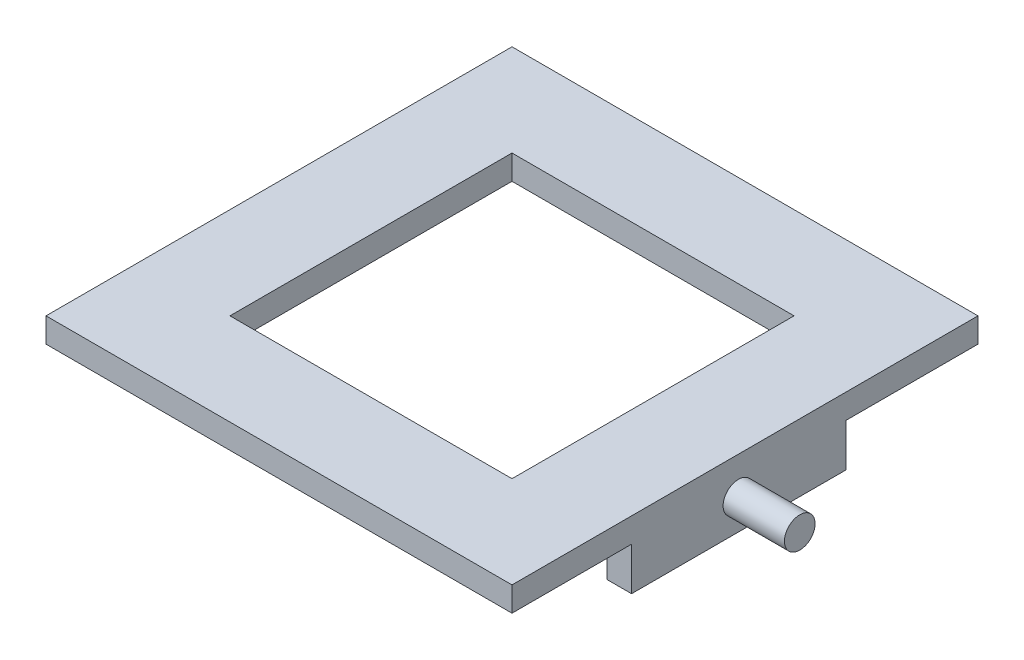
SolidWorks part; units mm, degrees
ref_plane "Front Plane" through (0, 0, 0) normal (0, 0, 1) x (1, 0, 0)
ref_plane "Top Plane" through (0, 0, 0) normal (0, 1, 0) x (1, 0, 0)
ref_plane "Right Plane" through (0, 0, 0) normal (1, 0, 0) x (0, 0, -1)
sketch "Sketch1" plane through (0, 0, 0) normal (0, 1, 0) x (1, 0, 0)
  line L0 (15, 15) -> (15, 61)
  line L1 (0, 0) -> (76, 0)
  line L2 (0, 0) -> (0, 76)
  line L3 (0, 76) -> (76, 76)
  line L4 (76, 0) -> (76, 76)
  line L5 (15, 61) -> (61, 61)
  line L6 (61, 15) -> (61, 61)
  line L7 (15, 15) -> (61, 15)
  dimension "D1" = 76
  dimension "D2" = 76
  dimension "D3" = 15
extrude "Boss-Extrude2" add sketch "Sketch1" along normal blind 4
sketch "Sketch3" plane through (0, 0, 0) normal (-1, 0, 0) x (0, 0, 1)
sketch "Sketch7" plane through (0, 0, 0) normal (-1, 0, 0) x (0, 0, 1)
  line L0 (-76, 4) -> (0, 4) construction
  line L1 (-54.5, 4) -> (-19.5, 4)
  line L2 (-54.5, 4) -> (-54.5, -7)
  line L3 (-54.5, -7) -> (-19.5, -7)
  line L4 (-19.5, 4) -> (-19.5, -7)
  line L9 (-51.45, -2.06) -> (-22.55, -2.06)
  circle A4 centre (-51.45, -2.06) radius 0.6
  circle A5 centre (-22.55, -2.06) radius 0.6
  point P6 (-37, -2.06)
  point P7 (-37, 4)
  point P13 (-36.7751, 4)
  point P25 (-76, 0)
  dimension "D9" = 1.2
  dimension "D10" = 1.2
  dimension "D4" = 17.5
  dimension "D5" = 6.06
  dimension "D3" = 28.9
  dimension "D1" = 19.5
  dimension "D2" = 35
  dimension "D11" = 11
extrude "Boss-Extrude5" add sketch "Sketch7" along normal blind 2 separate body contours A4 | A5
sketch "Sketch8" plane through (0, 0, 0) normal (-1, 0, 0) x (0, 0, 1)
  line L0 (-76, 4) -> (0, 4) construction
  line L1 (-54.5, 4) -> (-19.5, 4)
  line L2 (-54.5, 4) -> (-54.5, -7)
  line L3 (-54.5, -7) -> (-19.5, -7)
  line L4 (-19.5, 4) -> (-19.5, -7)
  dimension "D1" = 11
  dimension "D2" = 35
  dimension "D3" = 19.5
extrude "Boss-Extrude6" add sketch "Sketch8" against normal blind 4
sketch "Sketch9" plane through (76, 0, 0) normal (1, 0, 0) x (0, 0, -1)
  line L0 (0, 4) -> (76, 4) construction
  line L1 (19.5, -7) -> (54.5, -7)
  line L2 (19.5, -7) -> (19.5, 4)
  line L3 (19.5, 4) -> (54.5, 4)
  line L4 (54.5, -7) -> (54.5, 4)
  dimension "D1" = 35
extrude "Boss-Extrude7" add sketch "Sketch9" against normal blind 4
sketch "Sketch10" plane through (76, 0, 0) normal (1, 0, 0) x (0, 0, -1)
  line L0 (0, 4) -> (76, 4) construction
  circle A0 centre (36.93, -2.06) radius 2.5
  dimension "D1" = 5
  dimension "D2" = 36.93
  dimension "D3" = 6.06
extrude "Boss-Extrude8" add sketch "Sketch10" along normal blind 10
